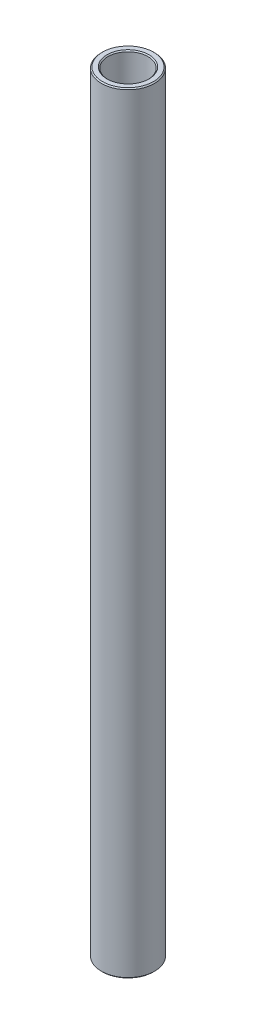
SolidWorks part; units mm, degrees
ref_plane "Front Plane" through (0, 0, 0) normal (0, 0, 1) x (1, 0, 0)
ref_plane "Top Plane" through (0, 0, 0) normal (0, 1, 0) x (1, 0, 0)
ref_plane "Right Plane" through (0, 0, 0) normal (1, 0, 0) x (0, 0, -1)
sketch "Sketch1" plane through (0, 0, 0) normal (0, 0, 1) x (1, 0, 0)
  line L0 (0, 11.6086) -> (0, -11.6086) construction
  line L1 (4.7625, 92.075) -> (6.35, 92.075)
  line L2 (6.35, 92.075) -> (6.35, -92.075)
  line L3 (6.35, -92.075) -> (4.7625, -92.075)
  line L4 (4.7625, -92.075) -> (4.7625, 92.075)
  line L5 (4.7625, 0) -> (0, 0) construction
  dimension "D1" = 9.525
  dimension "D2" = 12.7
  dimension "D3" = 184.15
revolve "Revolve1" add sketch "Sketch1" angle 360 about L0
chamfer "Chamfer1" distance 0.254 angle 45 4 edges at (-4.7625, -92.075, 0) (-6.35, -92.075, 0) (-6.35, 92.075, 0) (-4.7625, 92.075, 0)
